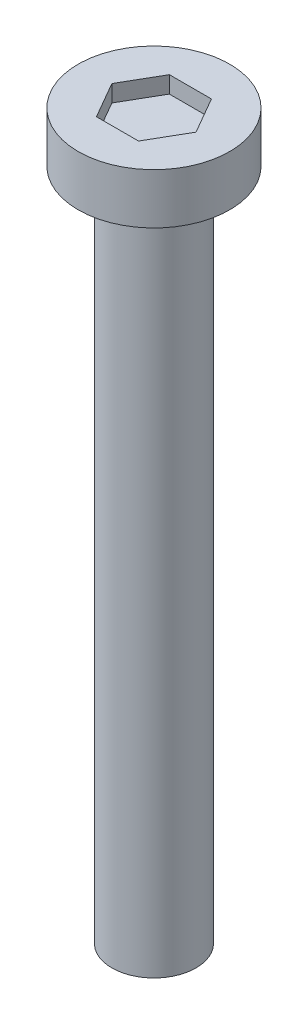
SolidWorks part; units mm, degrees
ref_plane "Front Plane" through (0, 0, 0) normal (0, 0, 1) x (1, 0, 0)
ref_plane "Top Plane" through (0, 0, 0) normal (0, 1, 0) x (1, 0, 0)
ref_plane "Right Plane" through (0, 0, 0) normal (1, 0, 0) x (0, 0, -1)
sketch "Sketch1" plane through (0, 0, 0) normal (0, 1, 0) x (1, 0, 0)
  circle A0 centre (0, 0) radius 1.25
  dimension "D1" = 2.5
extrude "Boss-Extrude1" add sketch "Sketch1" along normal blind 20
sketch "Sketch4" plane through (0, 20, 0) normal (0, 1, 0) x (1, 0, 0)
  circle A0 centre (0, 0) radius 2.25
  dimension "D1" = 4.5
extrude "Boss-Extrude2" add sketch "Sketch4" along normal blind 1.5
sketch "Sketch5" plane through (0, 21.5, 0) normal (0, 1, 0) x (1, 0, 0)
  line L1 (1.25, 0) -> (0.625, 1.0825)
  line L2 (0.625, 1.0825) -> (-0.625, 1.0825)
  line L3 (-0.625, 1.0825) -> (-1.25, 0)
  line L4 (-1.25, 0) -> (-0.625, -1.0825)
  line L5 (-0.625, -1.0825) -> (0.625, -1.0825)
  line L6 (0.625, -1.0825) -> (1.25, 0)
  circle A0 centre (0, 0) radius 1.0825 construction
  dimension "D1" = 1.25
extrude "Cut-Extrude1" cut sketch "Sketch5" against normal blind 0.5
thread "Thread1" pitch 0.7 start angle 0, offset 0, length 18, pitch 0.7, diameter 2.5
ref_plane "Plane1" through (1.25, 0, 0) normal (0, 0, 1) x (1, 0, 0)
sketch "Thread Profile1" plane through (1.25, 0, 0) normal (0, 0, 1) x (1, 0, 0)
  line L0 (0, 0) -> (0, 0.7) construction
  line L1 (0, 0) -> (0.3789, 0.2187)
  line L2 (0.3789, 0.2187) -> (0.3789, 0.3062)
  line L3 (0.3789, 0.3062) -> (0, 0.525)
  line L4 (0.3789, 0.2625) -> (0, 0.2625) construction
  line L11 (0, 0) -> (0, 0.525)
  point P2 (0, 0)
  dimension "Pitch" = 0.7
  dimension "Profile_Angle" = 60
  dimension "Profile_Land" = 0.0875
  dimension "Profile_Height" = 0.3789
